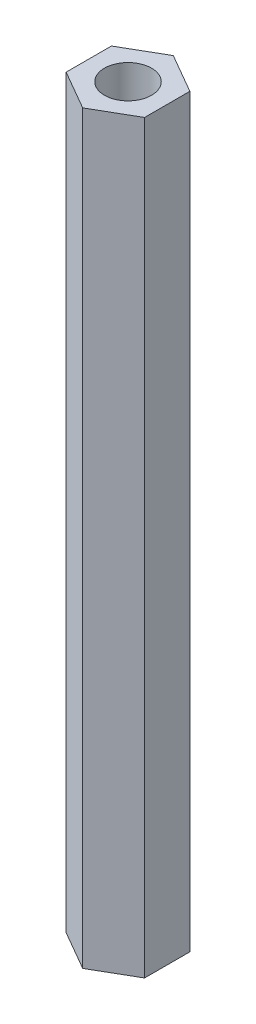
SolidWorks part; units mm, degrees
ref_plane "Спереди" through (0, 0, 0) normal (0, 0, 1) x (1, 0, 0)
ref_plane "Сверху" through (0, 0, 0) normal (0, 1, 0) x (1, 0, 0)
ref_plane "Справа" through (0, 0, 0) normal (1, 0, 0) x (0, 0, -1)
sketch "Эскиз1" plane through (0, 0, 0) normal (0, 1, 0) x (1, 0, 0)
  line L0 (0, 0) -> (0, 2.8868) construction
  line L1 (0, -2.8868) -> (2.5, -1.4434)
  line L2 (2.5, -1.4434) -> (2.5, 1.4434)
  line L3 (2.5, 1.4434) -> (0, 2.8868)
  line L4 (0, 2.8868) -> (-2.5, 1.4434)
  line L5 (-2.5, 1.4434) -> (-2.5, -1.4434)
  line L6 (-2.5, -1.4434) -> (0, -2.8868)
  circle A0 centre (0, 0) radius 2.5 construction
  circle A1 centre (0, 0) radius 1.5
  dimension "D2" = 3
  dimension "D1" = 5
extrude "Бобышка-Вытянуть1" add sketch "Эскиз1" along normal blind 47.5
